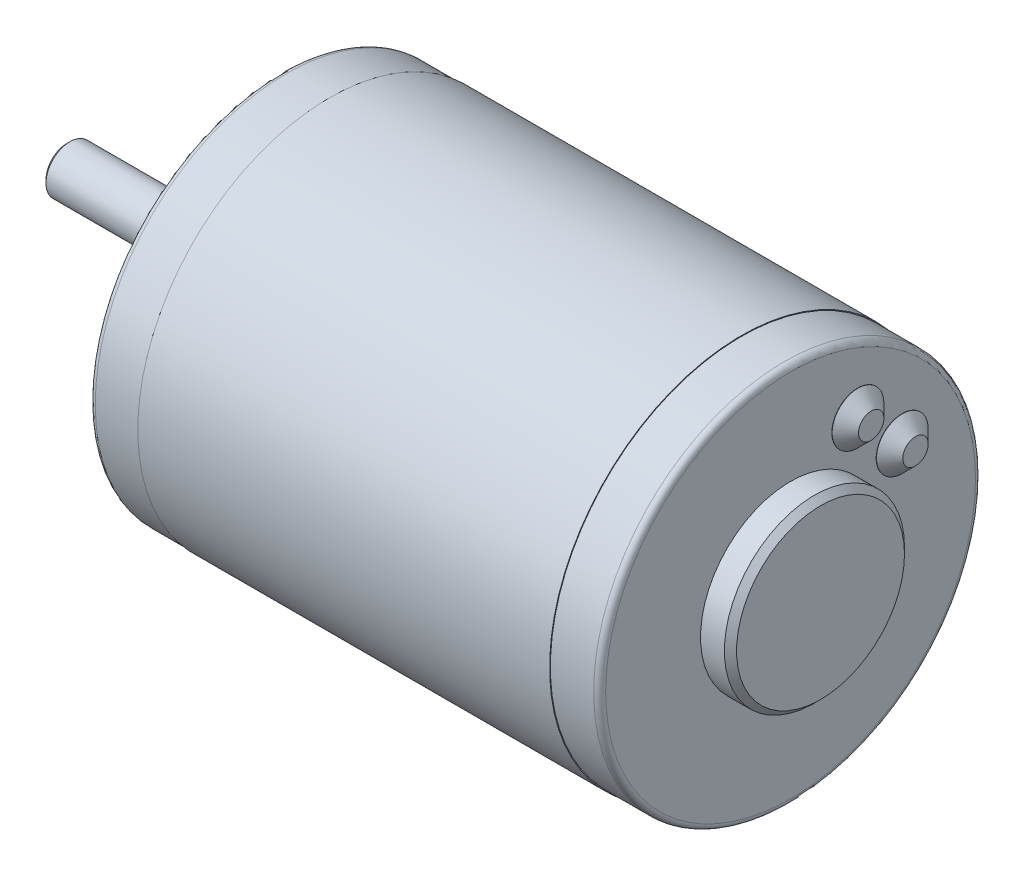
SolidWorks part; units mm, degrees
ref_plane "Front Plane" through (0, 0, 0) normal (0, 0, 1) x (1, 0, 0)
ref_plane "Top Plane" through (0, 0, 0) normal (0, 1, 0) x (1, 0, 0)
ref_plane "Right Plane" through (0, 0, 0) normal (1, 0, 0) x (0, 0, -1)
sketch "Sketch1" plane through (0, 0, 0) normal (0, 0, 1) x (1, 0, 0)
  line L0 (8.2296, 32.004) -> (8.2296, 0)
  line L1 (8.2296, 0) -> (76.9864, 0)
  line L2 (76.9864, 0) -> (76.9864, 32.004)
  line L3 (76.9864, 32.004) -> (8.2296, 32.004)
  line L4 (8.2296, 0) -> (76.9864, 0) construction
revolve "Revolve1" add sketch "Sketch1" angle 360 about L4
sketch "Sketch2" plane through (76.9864, 0, 0) normal (1, 0, 0) x (0, 0, -1)
  circle A0 centre (0, 0) radius 31.877
extrude "Boss-Extrude1" add sketch "Sketch2" along normal blind 8.2296
sketch "Sketch3" plane through (85.216, 0, 0) normal (1, 0, 0) x (0, 0, -1)
  circle A0 centre (0, 0) radius 15.0368
extrude "Boss-Extrude2" add sketch "Sketch3" along normal blind 5
sketch "Sketch4" plane through (8.2296, 0, 0) normal (-1, 0, 0) x (0, 0, 1)
  circle A0 centre (0, 0) radius 31.877
extrude "Boss-Extrude3" add sketch "Sketch4" along normal blind 8.2296
sketch "Sketch5" plane through (0, 0, 0) normal (-1, 0, 0) x (0, 0, 1)
  circle A0 centre (0, 0) radius 9.525
extrude "Boss-Extrude4" add sketch "Sketch5" along normal blind 4
sketch "Sketch6" plane through (-4, 0, 0) normal (-1, 0, 0) x (0, 0, 1)
  circle A0 centre (0, 0) radius 4
extrude "Boss-Extrude5" add sketch "Sketch6" along normal blind 31.6
ref_plane "Plane1" through (0, 2.8, 0) normal (0, -1, 0) x (1, 0, 0)
ref_plane "Plane2" through (0, 0, -18.6071) normal (0, 0, 1) x (1, 0, 0)
sketch "Sketch8" plane through (0, 0, -18.6071) normal (0, 0, 1) x (1, 0, 0)
  line L0 (85.216, 15.5254) -> (85.216, 11.2074)
  line L1 (85.216, 11.2074) -> (87.4639, 11.2074)
  line L2 (87.4639, 11.2074) -> (87.4639, 13.3254)
  line L3 (87.4639, 13.3254) -> (85.2639, 15.5254)
  line L4 (85.2639, 15.5254) -> (85.216, 15.5254)
  line L5 (85.216, 11.2074) -> (87.4639, 11.2074) construction
revolve "Revolve2" add sketch "Sketch8" angle 360 about L5
ref_plane "Plane3" through (0, 0, -11.2074) normal (0, 0, 1) x (1, 0, 0)
sketch "Sketch9" plane through (0, 0, -11.2074) normal (0, 0, 1) x (1, 0, 0)
  line L0 (85.216, 22.9251) -> (85.216, 18.6071)
  line L1 (85.216, 18.6071) -> (87.4639, 18.6071)
  line L2 (87.4639, 18.6071) -> (87.4639, 20.7251)
  line L3 (87.4639, 20.7251) -> (85.2639, 22.9251)
  line L4 (85.2639, 22.9251) -> (85.216, 22.9251)
  line L5 (85.216, 18.6071) -> (87.4639, 18.6071) construction
revolve "Revolve3" add sketch "Sketch9" angle 360 about L5
hole_wizard "#21 (0.159) Diameter Hole1" positions "Sketch11" profile "Sketch10" hole size "#21" standard "ANSI Inch"
sketch "Sketch11" plane through (0, 0, 0) normal (-1, 0, 0) x (0, 0, 1)
  point P0 (0, 25.4)
  point P1 (0, -25.4)
sketch "Sketch10" plane through (0, 25.4, 0) normal (0, 1, 0) x (0, 0, 1)
  line L0 (0, 0) -> (0, 14.8277)
  line L1 (0, 14.8277) -> (2.0193, 13.6144)
  line L2 (2.0193, 13.6144) -> (2.0193, 0)
  line L5 (2.0193, 0) -> (0, 0)
  line L10 (0, 14.8277) -> (-2.0193, 13.6144) construction
  line L11 (0, -6.35) -> (0, 107.95) construction
  dimension "Hole Dia." = 4.0386
  dimension "Hole Depth" = 13.6144
  dimension "Drill Angle" = 118
chamfer "Chamfer1" distance 1.016 angle 45 2 edges at (-4, 0, 9.525) (90.216, 0, -15.0368)
chamfer "Chamfer2" distance 0.5 angle 45 1 edges at (-35.6, 0, 4)
fillet "Fillet1" radius 1 2 edges at (0, 0, 31.877) (85.216, 0, -31.877)
